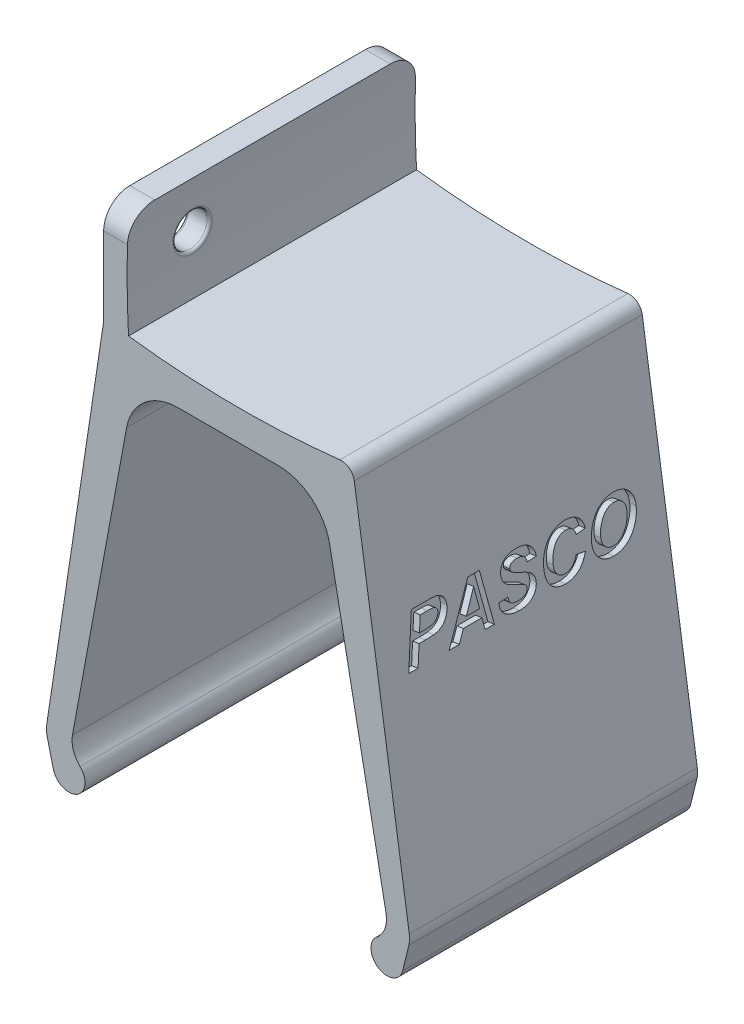
SolidWorks part; units mm, degrees
ref_plane "Front Plane" through (0, 0, 0) normal (0, 0, 1) x (1, 0, 0)
ref_plane "Top Plane" through (0, 0, 0) normal (0, 1, 0) x (1, 0, 0)
ref_plane "Right Plane" through (0, 0, 0) normal (1, 0, 0) x (0, 0, -1)
sketch "Sketch1" plane through (0, 0, 0) normal (0, 0, 1) x (1, 0, 0)
  line L0 (24.13, 0) -> (-24.13, 0)
  line L1 (-24.13, 0) -> (-35.3232, -74.2147)
  line L2 (-30.861, -82.423) -> (-15.0171, -82.423) construction
  line L3 (-35.3232, -74.2147) -> (-33.8941, -80.0438)
  line L4 (-30.861, -76.1772) -> (-18.1309, -7.2396)
  line L5 (-18.1309, -7.2396) -> (18.1309, -7.2396)
  line L6 (0, 13.3818) -> (0, -105.7494) construction
  line L7 (30.861, -82.423) -> (15.0171, -82.423) construction
  line L8 (31.4815, -76.2395) -> (18.1309, -7.2396)
  line L9 (35.3232, -74.2147) -> (33.8941, -80.0438)
  line L10 (24.13, 0) -> (35.3232, -74.2147)
  arc A0 (-33.8941, -80.0438) -> (-30.861, -76.1772) centre (-30.861, -79.3001) ccw
  arc A1 (33.8941, -80.0438) -> (31.4815, -76.2395) centre (30.861, -79.3001) cw
  point P0 (-35.5772, -74.2147)
  point P19 (0, -7.2396)
  point P21 (0, 0)
  dimension "D1" = 82.423
  dimension "D2" = 61.722
  dimension "D3" = 48.26
extrude "Boss-Extrude1" add sketch "Sketch1" along normal blind 55.88
sketch "Sketch2" plane through (0, 0, 0) normal (0, 1, 0) x (1, 0, 0)
  line L0 (24.13, -55.88) -> (-24.13, -55.88) construction
  line L1 (-24.13, 0) -> (-19.304, 0)
  line L2 (-24.13, 0) -> (-24.13, -55.88)
  line L3 (-24.13, -55.88) -> (-19.304, -55.88)
  line L4 (-19.304, 0) -> (-19.304, -55.88)
  dimension "D1" = 19.304
extrude "Boss-Extrude2" add sketch "Sketch2" along normal blind 20.32
sketch "Sketch3" plane through (-24.13, 0, 0) normal (-1, 0, 0) x (0, 0, 1)
  line L0 (55.88, 0) -> (0, 0) construction
  line L1 (55.88, 20.32) -> (55.88, 0) construction
  circle A0 centre (43.18, 11.176) radius 3.302
  dimension "D1" = 11.176
  dimension "D2" = 6.604
  dimension "D3" = 12.7
extrude "Cut-Extrude1" cut sketch "Sketch3" against normal through all
sketch "Sketch4" plane through (0, 0, 55.88) normal (0, 0, 1) x (1, 0, 0)
  line L0 (-19.304, 0) -> (24.13, 0)
  arc A0 (-19.304, 0) -> (24.13, 0) centre (2.413, 170.6574) ccw
extrude "Cut-Extrude2" cut sketch "Sketch4" against normal through all
fillet "Fillet1" radius 5.08 2 edges at (31.4815, -76.2395, 27.94) (-30.861, -76.1772, 27.94)
fillet "Fillet2" radius 5.08 2 edges at (-35.3232, -74.2147, 27.94) (35.3232, -74.2147, 27.94)
sketch "Sketch7" plane through (0, 0, 55.88) normal (0, 0, 1) x (1, 0, 0)
  line L0 (-19.304, 20.32) -> (-19.304, 0) construction
  line L1 (-19.304, 20.32) -> (-19.304, 0)
  arc A0 (-19.304, 20.32) -> (-19.304, 0) centre (167.6087, 10.16) ccw
extrude "Cut-Extrude5" cut sketch "Sketch7" against normal through all
fillet "Fillet3" radius 10.16 2 edges at (18.1309, -7.2396, 27.94) (-18.1309, -7.2396, 27.94)
fillet "Fillet4" radius 5.08 2 edges at (-21.717, 20.32, 0) (-21.717, 20.32, 55.88)
fillet "Fillet5" radius 2.54 1 edges at (24.13, 0, 27.94)
sketch "Sketch5" plane through (23.5933, 3.5584, 0) normal (0.9888, 0.1491, 0) x (0, 0, -1)
  text T0 "PASCO" font "Arial" height in points 36
extrude "Cut-Extrude3" cut sketch "Sketch5" against normal blind 1.27
sketch "Sketch6" plane through (-23.5933, 3.5584, 0) normal (-0.9888, 0.1491, 0) x (0, 0, 1)
  text T0 "Light Sensor\r\n   Bracket" font "Arial" height in points 22
extrude "Cut-Extrude4" cut sketch "Sketch6" against normal blind 1.27
fillet "Fillet7" radius 0.508 2 edges at (-24.13, 11.176, 46.482) (-19.5715, 11.9349, 39.9664)
